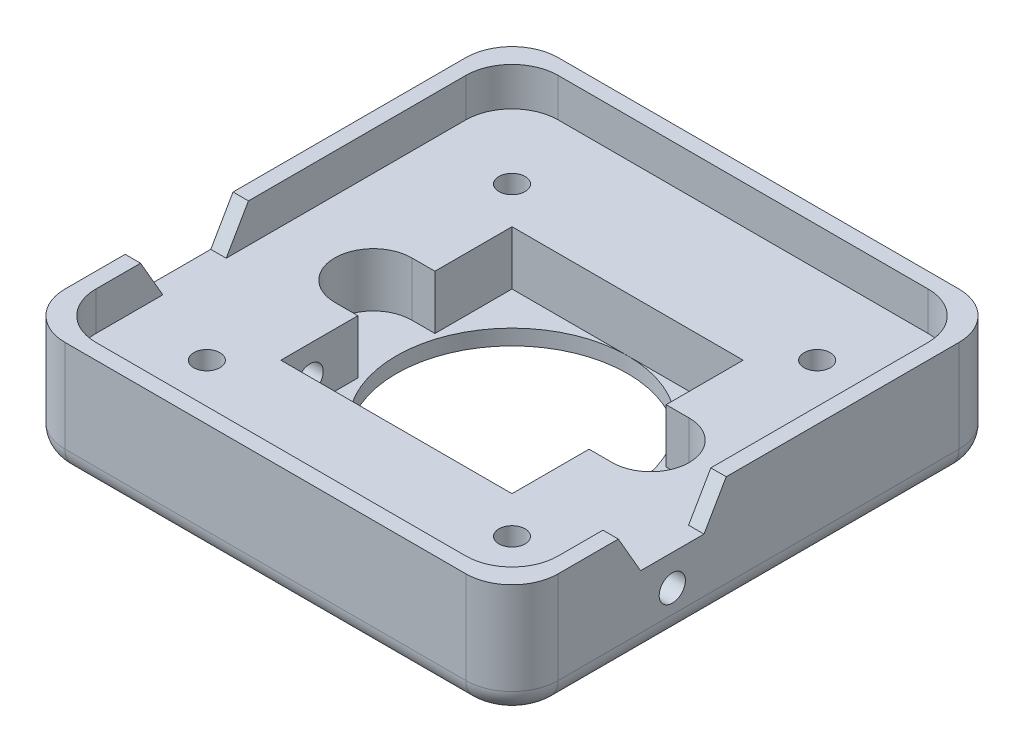
SolidWorks part; units mm, degrees
ref_plane "前视基准面" through (0, 0, 0) normal (0, 0, 1) x (1, 0, 0)
ref_plane "上视基准面" through (0, 0, 0) normal (0, 1, 0) x (1, 0, 0)
ref_plane "右视基准面" through (0, 0, 0) normal (1, 0, 0) x (0, 0, -1)
sketch "草图1" plane through (0, 0, 0) normal (0, 1, 0) x (1, 0, 0)
  line L0 (0, 19.3721) -> (0, 0) construction
  line L1 (-16, 16) -> (16, 16)
  line L2 (-16, 16) -> (-16, -16)
  line L3 (-16, -16) -> (16, -16)
  line L4 (16, 16) -> (16, -16)
  line L5 (0, 0) -> (-22.8001, 0) construction
  circle A0 centre (0, 0) radius 7.5
  dimension "D1" = 32
  dimension "D2" = 15
extrude "凸台-拉伸1" add sketch "草图1" along normal blind 5
sketch "草图2" plane through (0, 5, 0) normal (0, 1, 0) x (1, 0, 0)
  line L0 (0, 17.8836) -> (0, 0) construction
  line L1 (-7.5, 7.5) -> (7.5, 7.5)
  line L2 (-7.5, 7.5) -> (-7.5, 2.5)
  line L3 (-7.5, -7.5) -> (7.5, -7.5)
  line L4 (7.5, 7.5) -> (7.5, 2.5)
  line L5 (0, 0) -> (-23.6612, 0) construction
  line L6 (-9, 0) -> (9, 0) construction
  line L7 (-9, 2.5) -> (9, 2.5)
  line L8 (-9, -2.5) -> (9, -2.5)
  line L9 (-7.5, -2.5) -> (-7.5, -7.5)
  line L10 (7.5, -2.5) -> (7.5, -7.5)
  arc A0 (-9, 2.5) -> (-9, -2.5) centre (-9, 0) ccw
  arc A1 (9, -2.5) -> (9, 2.5) centre (9, 0) ccw
  point P10 (0, 0)
  dimension "D3" = 23
  dimension "D1" = 15
  dimension "D2" = 15
  dimension "D4" = 5
extrude "切除-拉伸1" cut sketch "草图2" against normal offset from surface (3.5 mm away) 1.5
sketch "草图3" plane through (0, 5, 0) normal (0, 1, 0) x (1, 0, 0)
  line L0 (15, 15) -> (-15, 15)
  line L1 (-15, 15) -> (-15, -15)
  line L2 (-15, -15) -> (15, -15)
  line L3 (15, -15) -> (15, 15)
  line L4 (-16, 16) -> (-16, -16)
  line L5 (-16, -16) -> (16, -16)
  line L6 (16, -16) -> (16, 16)
  line L7 (16, 16) -> (-16, 16)
  line L8 (-16, 16) -> (-16, -16)
  line L9 (-16, -16) -> (16, -16)
  line L10 (16, -16) -> (16, 16)
  line L11 (16, 16) -> (-16, 16)
  dimension "D2" = 0
  dimension "D3" = 1
extrude "凸台-拉伸2" add sketch "草图3" along normal blind 2.5
sketch "草图4" plane through (0, 0, 0) normal (0, -1, 0) x (1, 0, 0)
  line L0 (0, 17.3106) -> (0, 0) construction
  line L1 (-9.8995, 9.8995) -> (0, 0) construction
  circle A0 centre (-9.8995, 9.8995) radius 0.85
  circle A1 centre (9.8995, 9.8995) radius 0.85
  circle A2 centre (9.8995, -9.8995) radius 0.85
  circle A3 centre (-9.8995, -9.8995) radius 0.85
  point P14 (0, 0)
  dimension "D3" = 1.7
  dimension "D1" = 45
  dimension "D2" = 14
  dimension "D4" = 4
extrude "切除-拉伸2" cut sketch "草图4" against normal through all
sketch "草图5" plane through (0, 0, 0) normal (0, -1, 0) x (1, 0, 0)
  circle A0 centre (0, 0) radius 9
  dimension "D1" = 18
extrude "切除-拉伸3" cut sketch "草图5" against normal blind 0.5
fillet "圆角1" radius 3 8 edges at (-16, 3.75, -16) (-15, 6.25, -15) (15, 6.25, -15) (16, 3.75, -16) (16, 3.75, 16) (15, 6.25, 15) (-15, 6.25, 15) (-16, 3.75, 16)
sketch "草图6" plane through (0, 0, 0) normal (1, 0, 0) x (0, 0, -1)
  line L0 (0, 14.1213) -> (0, 0) construction
  line L1 (-13, 0) -> (13, 0) construction
  line L2 (-12, 5) -> (12, 5) construction
  line L3 (-12, 5) -> (12, 5) construction
  line L4 (-7.6566, 5) -> (-3.5434, 5)
  line L5 (-3.5434, 5) -> (-2.1, 7.5)
  line L6 (-13, 7.5) -> (13, 7.5) construction
  line L7 (-2.1, 7.5) -> (-9.1, 7.5)
  line L8 (-9.1, 7.5) -> (-7.6566, 5)
  line L9 (-5.6, 3) -> (-5.6, 12.4722) construction
  circle A0 centre (-5.6, 3) radius 0.85
  dimension "D1" = 1.7
  dimension "D2" = 3
  dimension "D3" = 5.6
  dimension "D4" = 120
  dimension "D5" = 7
extrude "切除-拉伸4" cut sketch "草图6" against normal through all and the other way through all
fillet "圆角2" radius 1.5 8 edges at (-15.1213, 0, -15.1213) (0, 0, -16) (15.1213, 0, -15.1213) (16, 0, 0) (15.1213, 0, 15.1213) (0, 0, 16) (-15.1213, 0, 15.1213) (-16, 0, 0)
